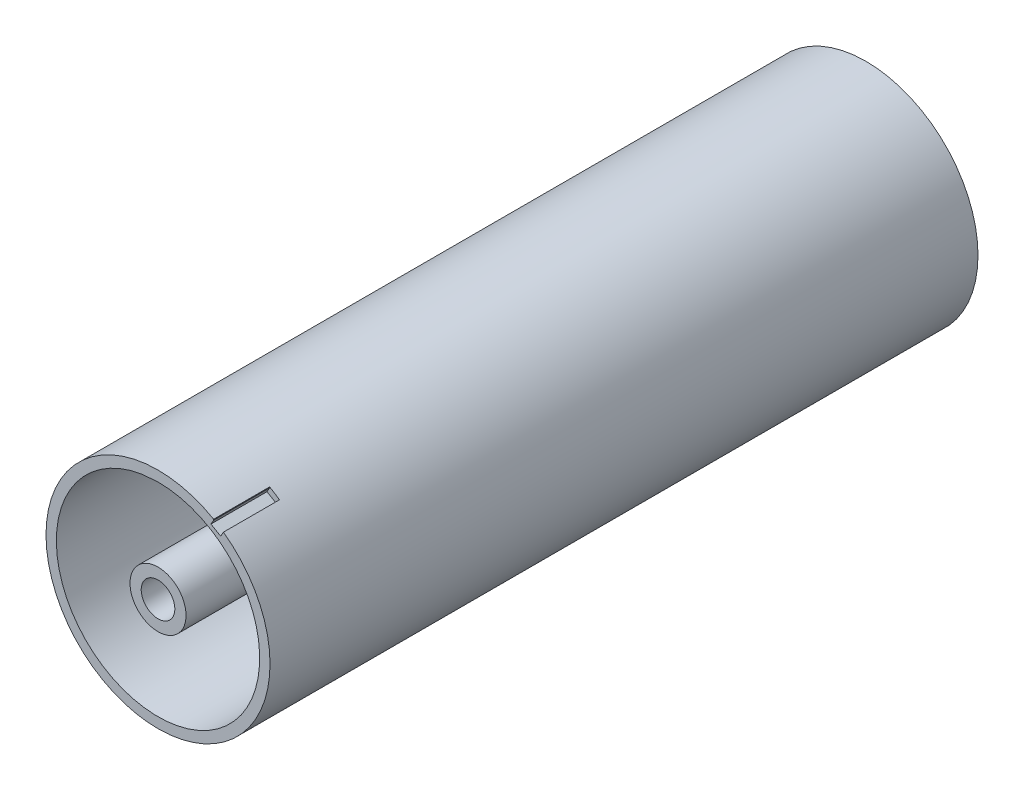
SolidWorks part; units mm, degrees
ref_plane "Спереди" through (0, 0, 0) normal (0, 0, 1) x (1, 0, 0)
ref_plane "Сверху" through (0, 0, 0) normal (0, 1, 0) x (1, 0, 0)
ref_plane "Справа" through (0, 0, 0) normal (1, 0, 0) x (0, 0, -1)
sketch "Эскиз2" plane through (0, 0, 0) normal (0, 0, 1) x (1, 0, 0)
  circle A0 centre (0, 0) radius 20
  circle A1 centre (0, 0) radius 18.15
  point P4 (0, 0)
  point P5 (0, 0)
  dimension "D1" = 40
  dimension "D2" = 36.3
extrude "Бобышка-Вытянуть1" add sketch "Эскиз2" along normal blind 126.4
sketch "Эскиз5" plane through (0, 0, 0) normal (0, 0, -1) x (-1, 0, 0)
  line L0 (0, 0) -> (0, 18.15) construction
  line L1 (0, 0) -> (2.9897, 17.9021) construction
  line L2 (0, 18.15) -> (0, 9.2195)
  line L3 (2.9897, 17.9021) -> (1.5187, 9.0936)
  circle A0 centre (0, 0) radius 18.15 construction
  arc A1 (0, 18.15) -> (2.9897, 17.9021) centre (0, 0) cw
  arc A2 (1.5187, 9.0936) -> (3.3803, 3.6842) centre (7.4367, 8.1053) ccw
  circle A3 centre (0, 0) radius 3
  arc A4 (-2.7273, 4.1907) -> (3.3803, 3.6842) centre (0, 0) ccw
  arc A5 (0, 9.2195) -> (-2.7273, 4.1907) centre (-6, 9.2195) cw
  point P16 (0, 5)
  dimension "D2" = 5
  dimension "D3" = 6
  dimension "D4" = 6
  dimension "D1" = 3
extrude "Бобышка-Вытянуть3" add sketch "Эскиз5" against normal through all
sketch "Sketch1" plane through (0, 0, 0) normal (0, 0, -1) x (-1, 0, 0)
  line L0 (0, 18.15) -> (2.9897, 17.9021)
  arc A2 (0, 18.15) -> (2.9897, 17.9021) centre (0, 0) ccw
  point P0 (0, 0)
extrude "Cut-Extrude1" cut sketch "Sketch1" against normal blind 59
sketch "Sketch2" plane through (0, 0, 126.4) normal (0, 0, 1) x (1, 0, 0)
  line L0 (0, 18.15) -> (-2.9897, 17.9021)
  arc A0 (-2.9897, 17.9021) -> (0, 18.15) centre (0, 0) ccw construction
  arc A2 (0, 18.15) -> (-2.9897, 17.9021) centre (0, 0) cw
  point P0 (1.0926, 18.1171)
  dimension "D1" = 18.15
extrude "Cut-Extrude2" cut sketch "Sketch2" against normal blind 59
sketch "Sketch4" plane through (0, 0, 126.4) normal (0, 0, 1) x (1, 0, 0)
  line L0 (0, 0) -> (0, 18.15) construction
  line L1 (0, 18.15) -> (9.075, 15.7184) construction
  line L2 (9.075, 15.7184) -> (0, 0) construction
  line L3 (9.075, 15.7184) -> (9.9499, 17.2337) construction
  line L4 (9.9499, 17.2337) -> (9.4499, 16.3677)
  line L5 (9.4499, 16.3677) -> (11.1819, 15.3677)
  line L6 (11.1819, 15.3677) -> (11.6819, 16.2337)
  circle A0 centre (0, 0) radius 18.15 construction
  circle A2 centre (0, 0) radius 20 construction
  arc A3 (9.9499, 17.2337) -> (11.6819, 16.2337) centre (11.2461, 17.4789) cw
  point P13 (0, 0)
  dimension "D2" = 2
  dimension "D1" = 30
  dimension "D3" = 1
sketch "Sketch3" plane through (0, 0, 126.4) normal (0, 0, 1) x (1, 0, 0)
  circle A0 centre (0, 0) radius 5
  circle A1 centre (0, 0) radius 3
  dimension "D1" = 10
  dimension "D2" = 6
extrude "Boss-Extrude1" add sketch "Sketch3" against normal offset from surface (58.6 mm away) 0.4 separate body up to face at (-0.7289, 8.7896, 67.4)
extrude "Cut-Extrude3" cut sketch "Sketch4" against normal blind 10
